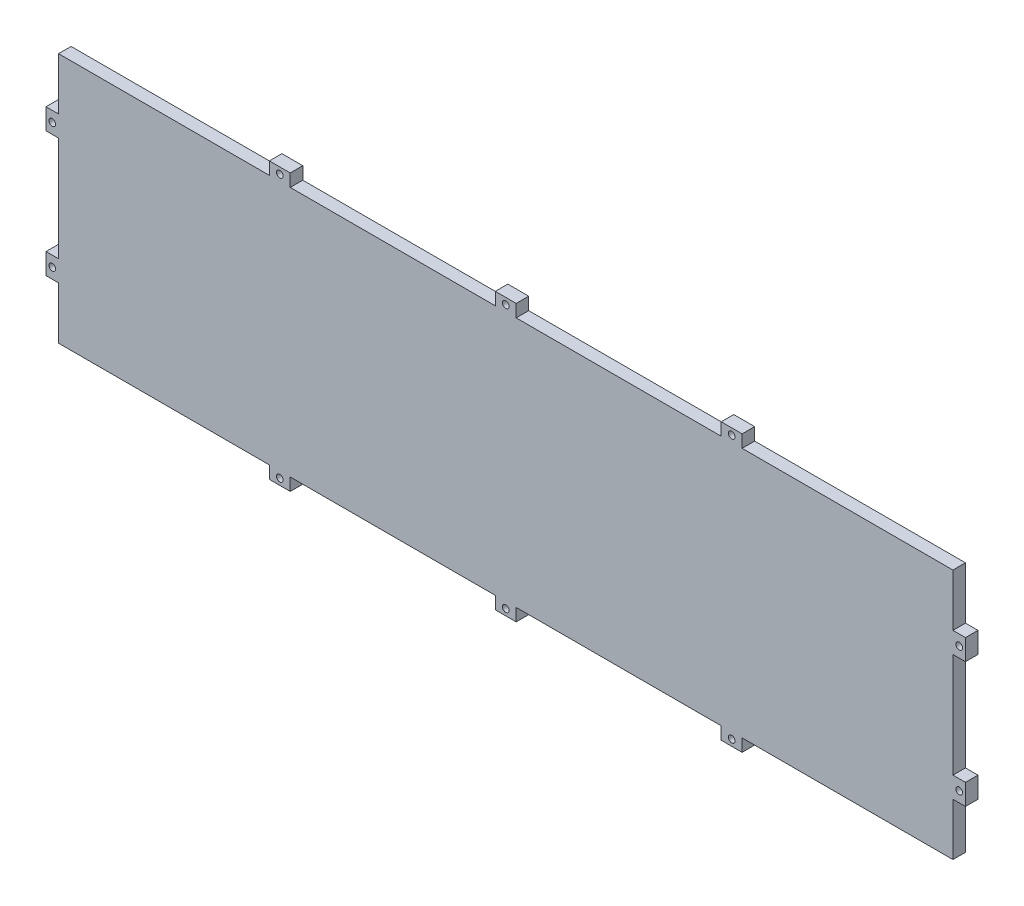
SolidWorks part; units mm, degrees
ref_plane "Front Plane" through (0, 0, 0) normal (0, 0, 1) x (1, 0, 0)
ref_plane "Top Plane" through (0, 0, 0) normal (0, 1, 0) x (1, 0, 0)
ref_plane "Right Plane" through (0, 0, 0) normal (1, 0, 0) x (0, 0, -1)
sketch "Sketch1" plane through (0, 0, 0) normal (0, 0, 1) x (1, 0, 0)
  line L0 (110.275, 146) -> (113.475, 146) construction
  line L1 (6, 269) -> (106.875, 269)
  line L2 (6, 269) -> (6, 244)
  line L3 (6, 149) -> (106.875, 149)
  line L4 (434, 269) -> (434, 244)
  line L5 (110.275, 149) -> (110.275, 143) construction
  line L6 (113.475, 143) -> (113.475, 149) construction
  line L7 (218.4, 146) -> (221.6, 146) construction
  line L8 (218.4, 149) -> (218.4, 143) construction
  line L9 (221.6, 143) -> (221.6, 149) construction
  line L10 (326.525, 146) -> (329.725, 146) construction
  line L11 (326.525, 149) -> (326.525, 143) construction
  line L12 (329.725, 143) -> (329.725, 149) construction
  line L13 (116.875, 149) -> (215, 149)
  line L14 (106.875, 143) -> (116.875, 143)
  line L15 (106.875, 143) -> (106.875, 149)
  line L16 (225, 149) -> (323.125, 149)
  line L17 (116.875, 143) -> (116.875, 149)
  line L18 (106.875, 143) -> (116.875, 149) construction
  line L19 (106.875, 149) -> (116.875, 143) construction
  line L20 (215, 143) -> (225, 143)
  line L21 (215, 143) -> (215, 149)
  line L22 (333.125, 149) -> (434, 149)
  line L23 (225, 143) -> (225, 149)
  line L24 (215, 143) -> (225, 149) construction
  line L25 (215, 149) -> (225, 143) construction
  line L26 (323.125, 143) -> (333.125, 143)
  line L27 (323.125, 143) -> (323.125, 149)
  line L28 (6, 209) -> (434, 209) construction
  line L29 (333.125, 143) -> (333.125, 149)
  line L30 (323.125, 143) -> (333.125, 149) construction
  line L31 (323.125, 149) -> (333.125, 143) construction
  line L32 (323.125, 275) -> (323.125, 269)
  line L33 (323.125, 275) -> (333.125, 275)
  line L34 (333.125, 275) -> (333.125, 269)
  line L35 (215, 275) -> (215, 269)
  line L36 (215, 275) -> (225, 275)
  line L37 (225, 275) -> (225, 269)
  line L38 (106.875, 275) -> (106.875, 269)
  line L39 (116.875, 275) -> (116.875, 269)
  line L40 (106.875, 275) -> (116.875, 275)
  line L41 (333.125, 269) -> (434, 269)
  line L42 (225, 269) -> (323.125, 269)
  line L43 (116.875, 269) -> (215, 269)
  line L44 (0, 269) -> (6, 209) construction
  line L45 (6, 234) -> (6, 184)
  line L46 (0, 234) -> (6, 234)
  line L47 (0, 234) -> (0, 244)
  line L48 (0, 244) -> (6, 244)
  line L49 (0, 269) -> (0, 244) construction
  line L50 (0, 234) -> (6, 244) construction
  line L51 (0, 244) -> (6, 234) construction
  line L52 (0, 174) -> (6, 174)
  line L53 (0, 184) -> (0, 174)
  line L54 (0, 184) -> (6, 184)
  line L55 (220, 209) -> (220, 221.6948) construction
  line L56 (440, 184) -> (434, 184)
  line L57 (440, 184) -> (440, 174)
  line L58 (440, 174) -> (434, 174)
  line L59 (440, 234) -> (434, 234)
  line L60 (440, 234) -> (440, 244)
  line L61 (440, 244) -> (434, 244)
  line L62 (6, 174) -> (6, 149)
  line L63 (434, 174) -> (434, 149)
  line L64 (434, 234) -> (434, 184)
  circle A0 centre (111.875, 146) radius 1.6
  circle A1 centre (220, 146) radius 1.6
  circle A2 centre (328.125, 146) radius 1.6
  circle A3 centre (328.125, 272) radius 1.6
  circle A4 centre (220, 272) radius 1.6
  circle A5 centre (111.875, 272) radius 1.6
  circle A6 centre (3, 239) radius 1.6
  circle A7 centre (3, 179) radius 1.6
  circle A8 centre (437, 239) radius 1.6
  circle A9 centre (437, 179) radius 1.6
  point P24 (111.875, 146)
  point P29 (220, 146)
  point P34 (328.125, 146)
  point P47 (106.875, 146)
  point P66 (106.875, 272)
  point P68 (3, 239)
  dimension "D3" = 3.2
  dimension "D1" = 10
  dimension "D2" = 10
extrude "Boss-Extrude1" add sketch "Sketch1" against normal blind 6 contours L2 L48 L47 L46 L45 L54 L53 L52 L62 L3 L15 L14 L17 L13 L21 L20 L23 L16 L27 L26 L29 L22 L63 L58 L57 L56 L64 L59 L60 L61 L4 L41 L34 L33 L32 L42 L37 L36 L35 L43 L39 L40 L38 L1
